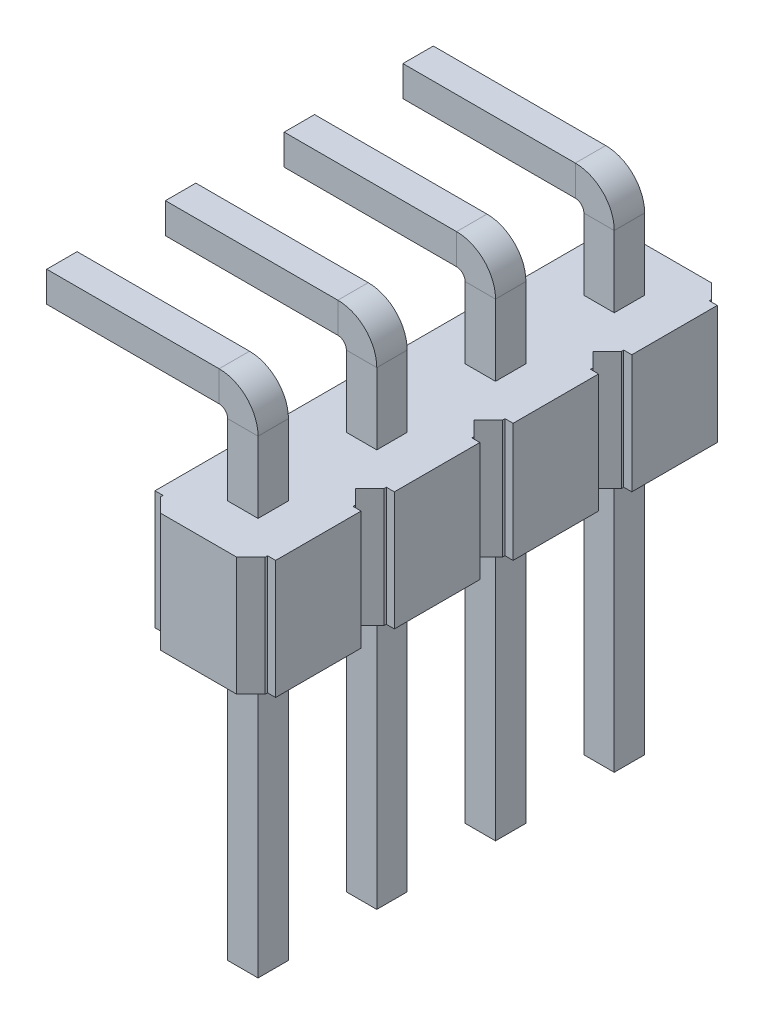
SolidWorks part; units mm, degrees
ref_plane "Front Plane" through (0, 0, 0) normal (0, 0, 1) x (1, 0, 0)
ref_plane "Top Plane" through (0, 0, 0) normal (0, 1, 0) x (1, 0, 0)
ref_plane "Right Plane" through (0, 0, 0) normal (1, 0, 0) x (0, 0, -1)
sketch "Sketch4" plane through (0, 0, 0) normal (0, 1, 0) x (1, 0, 0)
  line L0 (-2.37, -0.9) -> (-2.37, -0.95)
  line L3 (-0.47, 1.25) -> (-2.07, 1.25)
  line L4 (-2.54, 0.9) -> (-2.54, -0.9)
  line L6 (-2.37, 0.9) -> (-2.37, 0.95)
  line L7 (-2.37, 0.9) -> (-2.54, 0.9)
  line L9 (-2.07, 1.25) -> (-2.37, 0.95)
  line L10 (0, -0.9) -> (0, 0.9)
  line L12 (-0.47, 1.25) -> (-0.17, 0.95)
  line L13 (-0.17, 0.9) -> (-0.17, 0.95)
  line L14 (-0.17, 0.9) -> (0, 0.9)
  line L15 (-0.17, -0.9) -> (-0.17, -0.95)
  line L16 (-0.17, -0.9) -> (0, -0.9)
  line L17 (-0.47, -1.25) -> (-0.17, -0.95)
  line L18 (-0.47, -1.25) -> (-2.07, -1.25)
  line L19 (-2.07, -1.25) -> (-2.37, -0.95)
  line L20 (-2.37, -0.9) -> (-2.54, -0.9)
  point P8 (0, 0)
  point P15 (0, 0)
extrude "Boss-Extrude1" add sketch "Sketch4" along normal blind 2.5
sketch "Sketch6" plane through (0, 0, 0) normal (0, -1, 0) x (1, 0, 0)
  line L6 (-1.59, 0.32) -> (-1.59, -0.32)
  line L7 (-1.59, 0.32) -> (-0.95, 0.32)
  line L8 (-1.59, -0.32) -> (-0.95, -0.32)
  line L9 (-0.95, -0.32) -> (-0.95, 0.32)
  line L11 (1.59, 0.32) -> (1.59, -0.32)
  line L12 (1.59, -0.32) -> (0.95, -0.32)
  line L13 (0.95, -0.32) -> (0.95, 0.32)
  line L14 (1.59, 0.32) -> (0.95, 0.32)
  point P15 (-1.27, 0)
  point P18 (-1.27, 0.32)
extrude "Cut-Extrude1" cut sketch "Sketch6" against normal blind 2.5
ref_plane "Plane3" through (0, -6, 0) normal (0, 1, 0) x (1, 0, 0)
sketch "Sketch15" plane through (0, -6, 0) normal (0, 1, 0) x (1, 0, 0)
  line L0 (-1.59, 0.32) -> (-0.95, 0.32) construction
  line L1 (-0.95, 0.32) -> (-0.95, -0.32) construction
  line L2 (-0.95, -0.32) -> (-1.59, -0.32) construction
  line L3 (-1.59, -0.32) -> (-1.59, 0.32) construction
  line L4 (-1.59, 0.32) -> (-0.95, 0.32)
  line L5 (-0.95, 0.32) -> (-0.95, -0.32)
  line L6 (-0.95, -0.32) -> (-1.59, -0.32)
  line L7 (-1.59, -0.32) -> (-1.59, 0.32)
  line L8 (-1.59, 0) -> (-0.95, 0) construction
  line L9 (-0.95, 0) -> (-1.27, 0) construction
ref_plane "Plane4" through (0, 0, 0) normal (0, 0, -1) x (1, 0, 0)
sketch "Sketch17" plane through (0, 0, 0) normal (0, 0, -1) x (1, 0, 0)
  line L0 (-1.27, 6) -> (-1.27, -4)
  line L1 (-0.95, 6) -> (-1.59, 6) construction
  line L2 (-1.77, -4.5) -> (-5.52, -4.5)
  arc A0 (-1.77, -4.5) -> (-1.27, -4) centre (-1.77, -4) ccw
  point P7 (-1.27, -4.5)
  dimension "D3" = 0.5
  dimension "D1" = 10.5
  dimension "D2" = 4.25
sweep "Sweep1" add profiles "Sketch15" path "Sketch17"
chamfer "Chamfer4" distance 0.12 angle 45 8 edges at (-5.52, 4.5, -0.32) (-5.52, 4.82, 0) (-5.52, 4.5, 0.32) (-5.52, 4.18, 0) (-1.27, -6, 0.32) (-0.95, -6, 0) (-1.27, -6, -0.32) (-1.59, -6, 0)
pattern_linear "LPattern5" count 4 spacing 2.5 along (0, 0, 1) of "Boss-Extrude1", "Sweep1", "Chamfer4"
